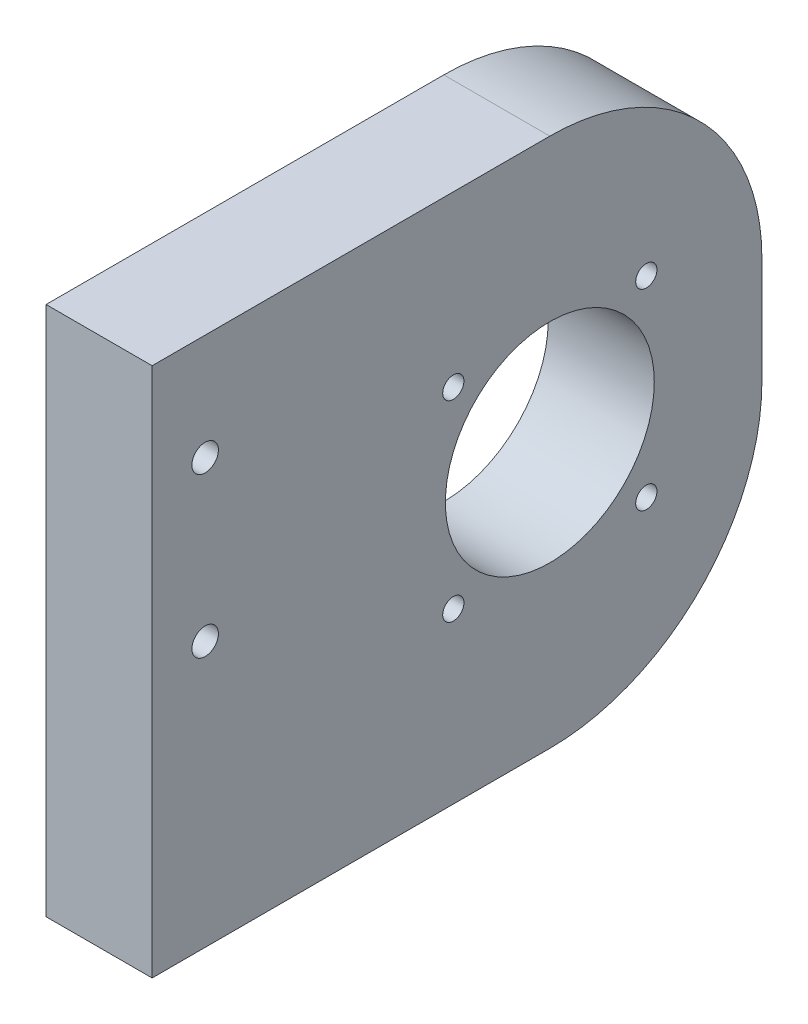
SolidWorks part; units mm, degrees
ref_plane "Front Plane" through (0, 0, 0) normal (0, 0, 1) x (1, 0, 0)
ref_plane "Top Plane" through (0, 0, 0) normal (0, 1, 0) x (1, 0, 0)
ref_plane "Right Plane" through (0, 0, 0) normal (1, 0, 0) x (0, 0, -1)
sketch "Sketch1" plane through (0, 0, 0) normal (0, 0, 1) x (1, 0, 0)
  line L1 (0, 0) -> (25.4, 0)
  line L2 (0, 0) -> (0, 127)
  line L3 (0, 127) -> (25.4, 127)
  line L4 (25.4, 0) -> (25.4, 127)
  dimension "D1" = 127
  dimension "D2" = 25.4
extrude "Boss-Extrude1" add sketch "Sketch1" along normal blind 146.05
fillet "Fillet1" radius 50.8 2 edges at (12.7, 0, 0) (12.7, 127, 0)
sketch "Sketch3" plane through (25.4, 0, 0) normal (1, 0, 0) x (0, 0, -1)
  line L0 (-146.05, 63.5) -> (-50.8, 63.5) construction
  line L1 (-146.05, 0) -> (-146.05, 127) construction
  line L2 (-146.05, 127) -> (-133.35, 127)
  line L3 (-73.914, 40.513) -> (-27.686, 40.513) construction
  line L4 (-73.914, 40.513) -> (-73.914, 86.487) construction
  line L5 (-73.914, 86.487) -> (-27.686, 86.487) construction
  line L6 (-27.686, 40.513) -> (-27.686, 86.487) construction
  line L7 (-73.914, 40.513) -> (-27.686, 86.487) construction
  line L8 (-73.914, 86.487) -> (-27.686, 40.513) construction
  line L9 (-146.05, 127) -> (-50.8, 127) construction
  line L12 (-133.35, 101.6) -> (-133.35, 63.5)
  circle A0 centre (-50.8, 63.5) radius 25.019
  circle A1 centre (-73.914, 86.487) radius 2.54
  circle A2 centre (-27.686, 86.487) radius 2.54
  circle A3 centre (-27.686, 40.513) radius 2.54
  circle A4 centre (-73.914, 40.513) radius 2.54
  circle A5 centre (-133.35, 63.5) radius 3.175
  circle A6 centre (-133.35, 101.6) radius 3.175
  dimension "D2" = 50.038
  dimension "D5" = 5.08
  dimension "D6" = 5.08
  dimension "D7" = 5.08
  dimension "D8" = 5.08
  dimension "D11" = 6.35
  dimension "D12" = 6.35
  dimension "D1" = 95.25
  dimension "D3" = 45.974
  dimension "D4" = 46.228
  dimension "D9" = 12.7
  dimension "D10" = 38.1
extrude "Cut-Extrude1" cut sketch "Sketch3" against normal up to surface (25.4 mm away)
